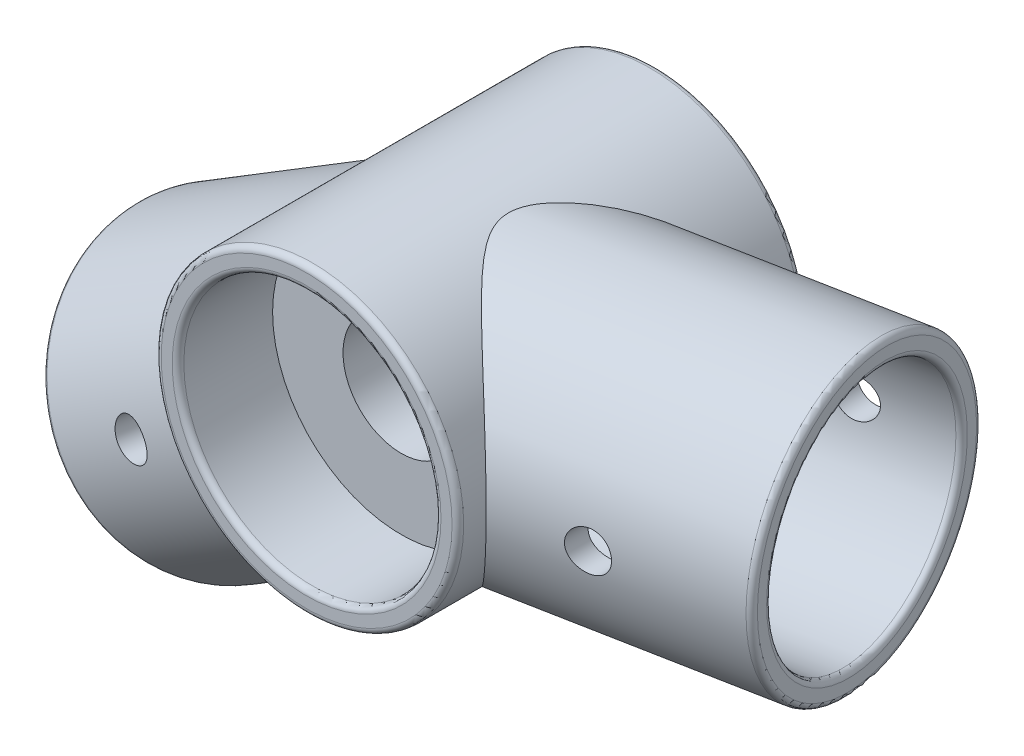
SolidWorks part; units mm, degrees
ref_plane "Front Plane" through (0, 0, 0) normal (0, 0, 1) x (1, 0, 0)
ref_plane "Top Plane" through (0, 0, 0) normal (0, 1, 0) x (1, 0, 0)
ref_plane "Right Plane" through (0, 0, 0) normal (1, 0, 0) x (0, 0, -1)
sketch "Sketch2" plane through (0, 0, 0) normal (0, 0, 1) x (1, 0, 0)
  circle A0 centre (0, 0) radius 13
  dimension "D1" = 26
extrude "Boss-Extrude2" add sketch "Sketch2" along normal mid plane 30
sketch "Sketch5" plane through (0, 0, 15) normal (0, 0, 1) x (1, 0, 0)
  circle A0 centre (0, 0) radius 5
  dimension "D1" = 10
extrude "Cut-Extrude2" cut sketch "Sketch5" against normal through all
sketch "Sketch3" [suppressed] plane through (0, 0, 0) normal (0, 0, 1) x (1, 0, 0)
  line L0 (0, 0) -> (-24.0896, 6.6852) construction
  dimension "D1" = 15.51
  dimension "D2" = 25
ref_plane "Plane1" [suppressed] through (-24.0896, 6.6852, 0) normal (-0.9636, 0.2674, 0) x (0, 0, 1)
sketch "Sketch1" [suppressed] plane through (-25.4465, 1.7956, 0) normal (0.9636, -0.2674, 0) x (0, 0, -1)
  circle A0 centre (0, 5.0743) radius 10.35
  circle A1 centre (0, 5.0743) radius 12.35
  dimension "D1" = 20.7
  dimension "D2" = 2
extrude "Boss-Extrude4" [suppressed] add sketch "Sketch1" along normal up to surface (17.1338 mm away)
sketch "Sketch4" plane through (0, 0, 15) normal (0, 0, -1) x (-1, 0, 0)
  circle A0 centre (0, 0) radius 11.05
  dimension "D1" = 22.1
extrude "Cut-Extrude1" [suppressed] cut sketch "Sketch4" along normal blind 8.128
fillet "Fillet1" [suppressed] radius 0.5
sketch "Sketch11" [suppressed] plane through (0, 0, 0) normal (0, 0, 1) x (1, 0, 0)
  line L2 (-20.3053, 18.4517) -> (-26.9103, -5.3488) construction
  line L3 (-23.6078, 6.5515) -> (-12.5266, 3.4763) construction
  arc A1 (-0.609, 12.9857) -> (-7.2139, -10.8148) centre (0, 0) ccw construction
  circle A2 centre (-18.0672, 5.0139) radius 1.7
  point P4 (-18.0672, 5.0139)
  dimension "D1" = 3.4
extrude "Cut-Extrude4" [suppressed] cut sketch "Sketch11" against normal through all both and the other way through all contours A2
sketch "Sketch14" plane through (0, 0, 0) normal (0, 0, 1) x (1, 0, 0)
  line L0 (0, 0) -> (0, -50000) construction
ref_plane "Plane7" through (0, 0, 0) normal (-0.1736, 0, -0.9848) x (0, -1, 0)
sketch "Sketch6" plane through (0, 0, 0) normal (0.1736, 0, 0.9848) x (0.9848, 0, -0.1736)
  line L0 (0, 0) -> (-24.9266, -16.6932) construction
  dimension "D1" = 30
  dimension "D2" = 33.81
ref_plane "Plane2" through (-24.5479, -16.6932, 4.3285) normal (-0.8183, -0.5564, 0.1443) x (0.1166, 0.085, 0.9895)
sketch "Sketch7" plane through (-24.5479, -16.6932, 4.3285) normal (-0.8183, -0.5564, 0.1443) x (0.1166, 0.085, 0.9895)
  line L0 (-16.7189, 0) -> (12.9675, 0) construction
  circle A0 centre (-1.8757, 0) radius 10.35
  circle A1 centre (-1.8757, 0) radius 12.35
  ellipse E0 centre (-14.8429, 0.0703) end of major axis (-14.9044, -12.9296) minor radius 1.8757 construction
  ellipse E1 centre (14.8429, -0.0703) end of major axis (14.7813, -13.0701) minor radius 1.8757 construction
  point P6 (-1.8757, 0)
  dimension "D1" = 20.7
  dimension "D2" = 2
extrude "Boss-Extrude5" add sketch "Sketch7" against normal up to surface (22.3359 mm away)
sketch "Sketch13" plane through (0, 0, 0) normal (0, 0, 1) x (1, 0, 0)
  line L0 (0, 0) -> (0, -50000) construction
ref_plane "Plane6" through (0, 0, 0) normal (0.1876, 0, -0.9822) x (0, -1, 0)
sketch "Sketch8" plane through (0, 0, 0) normal (-0.1876, 0, 0.9822) x (0.9822, 0, 0.1876)
  line L0 (0, 0) -> (30, 0) construction
  dimension "D1" = 0
  dimension "D2" = 30
ref_plane "Plane3" through (29.4673, 0, 5.6281) normal (0.9822, 0, 0.1876) x (0.1876, 0, -0.9822)
sketch "Sketch9" plane through (29.4673, 0, 5.6281) normal (0.9822, 0, 0.1876) x (0.1876, 0, -0.9822)
  line L0 (-12.2948, 0) -> (17.1725, 0) construction
  circle A0 centre (2.4389, 0) radius 10.35
  circle A1 centre (2.4389, 0) radius 12.35
  ellipse E1 centre (-14.7337, 0) end of major axis (-14.7337, 13) minor radius 2.4389 construction
  ellipse E2 centre (14.7337, 0) end of major axis (14.7337, 13) minor radius 2.4389 construction
  dimension "D1" = 20.7
  dimension "D2" = 2
extrude "Boss-Extrude6" add sketch "Sketch9" against normal up to surface (19.2076 mm away)
sketch "Sketch10" plane through (0, 0, -15) normal (0, 0, 1) x (1, 0, 0)
  circle A0 centre (0, 0) radius 11.05
  dimension "D1" = 22.1
extrude "Cut-Extrude3" cut sketch "Sketch10" along normal blind 8.128
fillet "Fillet3" radius 0.5 4 edges at (-18.9467, -25.4113, 2.4724) (-17.822, -27.0652, 2.4724) (32.2418, 0, -8.8981) (31.8666, 0, -6.9337)
fillet "Fillet4" radius 0.5 4 edges at (13, 0, -15) (13, 0, 15) (5, 0, 15) (11.05, 0, -15)
sketch "Sketch12" plane through (0, 0, 0) normal (0, 0, 1) x (1, 0, 0)
  line L0 (27.7018, 0) -> (13, 0) construction
  circle A3 centre (20.3509, 0) radius 1.7
  circle A4 centre (0, 0) radius 13 construction
  circle A5 centre (0, 0) radius 13 construction
  ellipse E0 centre (29.9249, 0) end of major axis (29.9249, -11.85) minor radius 2.2231 construction
  ellipse E1 centre (29.9249, 0) end of major axis (29.9249, -11.85) minor radius 2.2231 construction
  dimension "D1" = 3.4
extrude "Cut-Extrude5" cut sketch "Sketch12" against normal through all both and the other way through all
sketch "Sketch15" plane through (0, 0, 0) normal (-0.1736, 0, -0.9848) x (0, -1, 0)
  line L0 (0, 0) -> (16.5745, 24.4043) construction
  line L1 (26.836, 17.5323) -> (6.3131, 31.2764) construction
  line L2 (16.5745, 24.4043) -> (6.2869, 9.2569) construction
  circle A0 centre (11.4307, 16.8306) radius 1.7
  dimension "D1" = 3.4
extrude "Cut-Extrude6" cut sketch "Sketch15" against normal through all both and the other way through all
ref_plane "Plane4" [suppressed] through (13, 0, 0) normal (1, 0, 0) x (0, 0, -1)
mirror "Mirror2" [suppressed] about plane through (13, 0, 0) normal (1, 0, 0)
delete or keep bodies "Body-Delete/Keep 1" [suppressed] type delete bodies bodies 111
ref_plane "Plane5" through (0, 0, -20) normal (0, 0, 1) x (1, 0, 0)
mirror "Mirror3" about plane through (0, 0, -20) normal (0, 0, 1) of bodies 120 112
delete or keep bodies "Body-Delete/Keep 2" type delete bodies bodies 120
move or copy body "Body-Move/Copy1" [suppressed] bodies to move or copy 116 placed by mates yes parameters "D1"=0, "D2"=0, "D3"=0
move or copy body "Body-Move/Copy2" bodies to move or copy 117 placed by mates yes parameters "D1"=0, "D2"=0, "D3"=0
